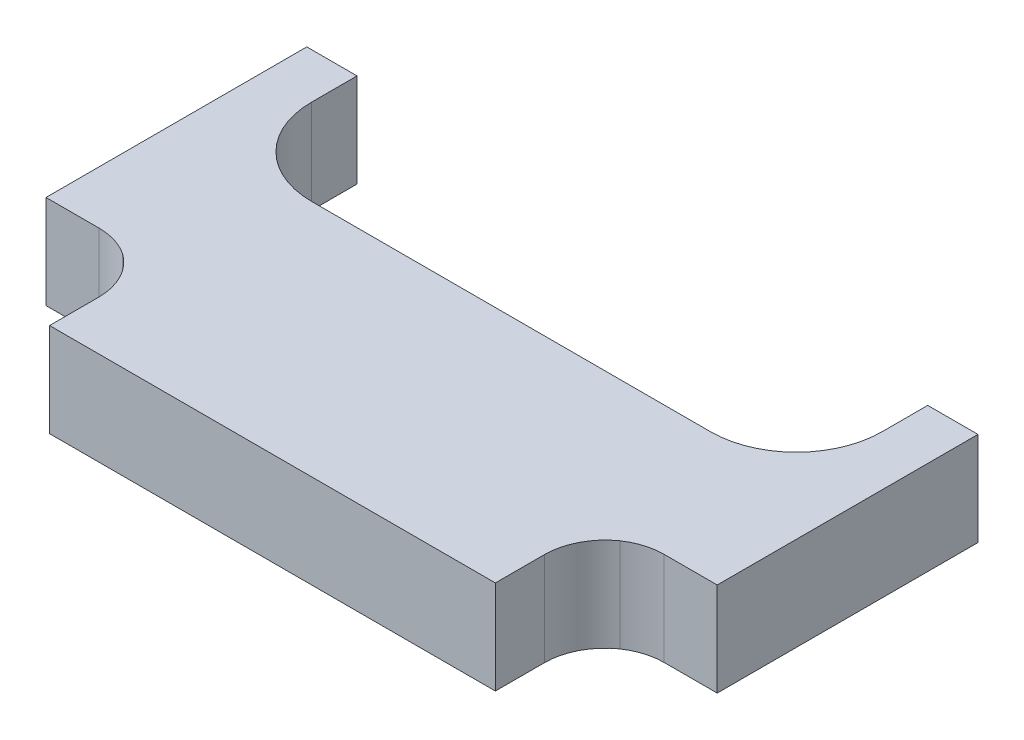
SolidWorks part; units mm, degrees
ref_plane "Plano frontal" through (0, 0, 0) normal (0, 0, 1) x (1, 0, 0)
ref_plane "Plano superior" through (0, 0, 0) normal (0, 1, 0) x (1, 0, 0)
ref_plane "Plano direito" through (0, 0, 0) normal (1, 0, 0) x (0, 0, -1)
sketch "Sketch3" plane through (0, 0, 0) normal (0, 1, 0) x (1, 0, 0)
  line L0 (-10.75, 5.925) -> (-10.75, -5.925) construction
  point P1 (0, 1.715)
  point P7 (-10.75, 0)
  line B0 (6.39, 1.715) -> (-6.39, 1.715)
  line B1 (-9.14, 4.465) -> (-9.14, 5.925)
  line B2 (-10.75, 5.925) -> (-9.14, 5.925)
  line B3 (-10.75, 5.925) -> (-10.75, -2.4289)
  line B4 (-10.75, -2.4289) -> (-9.0533, -2.4289)
  arc B5 (-7.9638, -2.7616) -> (-9.0533, -2.4289) centre (-9.0533, -4.3789) ccw
  arc B6 (-7.14, -4.3536) -> (-7.9638, -2.7616) centre (-9.09, -4.3536) ccw
  line B7 (-7.14, -4.3536) -> (-7.14, -5.925)
  line B8 (-7.14, -5.925) -> (7.14, -5.925)
  line B9 (7.14, -5.925) -> (7.14, -4.3536)
  arc B10 (7.9638, -2.7616) -> (7.14, -4.3536) centre (9.09, -4.3536) ccw
  arc B11 (9.0533, -2.4289) -> (7.9638, -2.7616) centre (9.0533, -4.3789) ccw
  line B12 (9.0533, -2.4289) -> (10.75, -2.4289)
  line B13 (10.75, -2.4289) -> (10.75, 5.925)
  line B14 (10.75, 5.925) -> (9.14, 5.925)
  line B15 (9.14, 5.925) -> (9.14, 4.465)
  arc B16 (6.39, 1.715) -> (9.14, 4.465) centre (6.39, 4.465) ccw
  arc B17 (-9.14, 4.465) -> (-6.39, 1.715) centre (-6.39, 4.465) ccw
sketch_block_instance "Dente Esteira - Engrenagem-1"
sketch_block "Dente Esteira - Engrenagem"
other "DetailItem3"
other "DetailItem4"
extrude "Boss-Extrude1" add sketch "Sketch3" along normal mid plane 3
